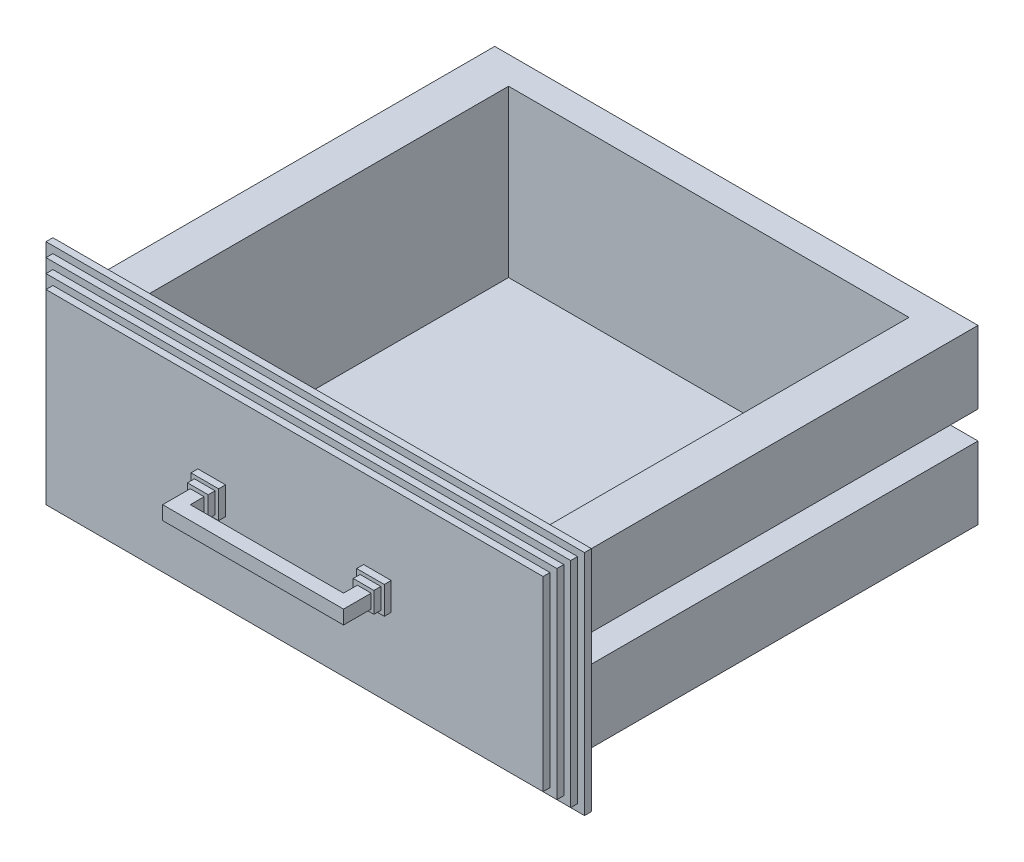
SolidWorks part; units mm, degrees
ref_plane "Front Plane" through (0, 0, 0) normal (0, 0, 1) x (1, 0, 0)
ref_plane "Top Plane" through (0, 0, 0) normal (0, 1, 0) x (1, 0, 0)
ref_plane "Right Plane" through (0, 0, 0) normal (1, 0, 0) x (0, 0, -1)
sketch "Sketch1" plane through (0, 0, 0) normal (0, 0, 1) x (1, 0, 0)
  line L0 (0, -415.8097) -> (0, 415.8097) construction
  line L1 (-175, 206.3609) -> (175, 206.3609)
  line L2 (-175, 206.3609) -> (-175, 258.8609)
  line L3 (-175, 331.3609) -> (175, 331.3609)
  line L4 (175, 206.3609) -> (175, 258.8609)
  line L5 (175, 258.8609) -> (155, 258.8609)
  line L6 (-175, 278.8609) -> (-155, 278.8609)
  line L7 (-175, 258.8609) -> (-155, 258.8609)
  line L8 (-155, 278.8609) -> (-155, 258.8609)
  line L9 (155, 278.8609) -> (155, 258.8609)
  line L10 (175, 278.8609) -> (155, 278.8609)
  line L11 (-175, 278.8609) -> (-175, 331.3609)
  line L12 (175, 278.8609) -> (175, 331.3609)
  dimension "D1" = 125
  dimension "D2" = 20
  dimension "D3" = 20
  dimension "D4" = 52.5
extrude "Boss-Extrude1" add sketch "Sketch1" along normal blind 320
sketch "Sketch2" plane through (0, 0, 320) normal (0, 0, 1) x (1, 0, 0)
  line L0 (0, 331.3609) -> (0, 206.3609) construction
  line L1 (175, 331.3609) -> (-175, 331.3609) construction
  line L2 (-175, 206.3609) -> (175, 206.3609) construction
  line L3 (-175, 278.8609) -> (155, 278.8609) construction
  line L4 (155, 258.8609) -> (-175, 258.8609) construction
  line L5 (70, 258.8609) -> (50, 258.8609)
  line L6 (-70, 278.8609) -> (-50, 278.8609)
  line L7 (-70, 278.8609) -> (-70, 258.8609)
  line L8 (-70, 258.8609) -> (-50, 258.8609)
  line L9 (-50, 278.8609) -> (-50, 258.8609)
  line L10 (50, 278.8609) -> (50, 258.8609)
  line L11 (70, 278.8609) -> (50, 278.8609)
  line L12 (70, 278.8609) -> (70, 258.8609)
  dimension "D1" = 20
  dimension "D2" = 50
extrude "Boss-Extrude2" add sketch "Sketch2" along normal blind 5
sketch "Sketch3" plane through (0, 0, 325) normal (0, 0, 1) x (1, 0, 0)
  line L0 (0, 331.3609) -> (0, 206.3609) construction
  line L1 (175, 331.3609) -> (-175, 331.3609) construction
  line L2 (-175, 206.3609) -> (175, 206.3609) construction
  line L3 (-161.3907, 268.8609) -> (0, 268.8609) construction
  line L4 (-60, 289.8862) -> (-60, 252.4462) construction
  line L5 (52.5, 276.3609) -> (67.5, 276.3609)
  line L6 (-52.5, 261.3609) -> (-67.5, 261.3609)
  line L7 (-52.5, 261.3609) -> (-52.5, 276.3609)
  line L8 (-52.5, 276.3609) -> (-67.5, 276.3609)
  line L9 (-67.5, 261.3609) -> (-67.5, 276.3609)
  line L10 (-52.5, 261.3609) -> (-67.5, 276.3609) construction
  line L11 (-52.5, 276.3609) -> (-67.5, 261.3609) construction
  line L12 (67.5, 261.3609) -> (67.5, 276.3609)
  line L13 (52.5, 261.3609) -> (67.5, 261.3609)
  line L14 (52.5, 261.3609) -> (52.5, 276.3609)
  point P10 (-60, 268.8609)
  dimension "D1" = 15
  dimension "D2" = 15
extrude "Boss-Extrude3" add sketch "Sketch3" along normal blind 5
sketch "Sketch4" plane through (0, 0, 330) normal (0, 0, 1) x (1, 0, 0)
  line L0 (0, 331.3609) -> (0, 206.3609) construction
  line L1 (175, 331.3609) -> (-175, 331.3609) construction
  line L2 (-175, 206.3609) -> (175, 206.3609) construction
  line L3 (-188.8492, 268.8609) -> (183.7972, 268.8609) construction
  line L4 (-60.4961, 250.6327) -> (-60.4961, 286.6802) construction
  line L5 (55.4961, 273.6564) -> (65.4961, 273.6564)
  line L6 (-55.4961, 263.6564) -> (-65.4961, 263.6564)
  line L7 (-55.4961, 263.6564) -> (-55.4961, 273.6564)
  line L8 (-55.4961, 273.6564) -> (-65.4961, 273.6564)
  line L9 (-65.4961, 263.6564) -> (-65.4961, 273.6564)
  line L10 (-55.4961, 263.6564) -> (-65.4961, 273.6564) construction
  line L11 (-55.4961, 273.6564) -> (-65.4961, 263.6564) construction
  line L12 (65.4961, 263.6564) -> (65.4961, 273.6564)
  line L13 (55.4961, 263.6564) -> (65.4961, 263.6564)
  line L14 (55.4961, 263.6564) -> (55.4961, 273.6564)
  point P10 (-60.4961, 268.6564)
  dimension "D1" = 10
  dimension "D2" = 10
extrude "Boss-Extrude4" add sketch "Sketch4" along normal blind 20
sketch "Sketch5" plane through (55.4961, 0, 0) normal (-1, 0, 0) x (0, 0, 1)
  line L0 (350, 263.6564) -> (330, 263.6564) construction
  line L1 (350, 273.6564) -> (340, 273.6564)
  line L2 (350, 273.6564) -> (350, 263.6564)
  line L3 (350, 263.6564) -> (340, 263.6564)
  line L4 (340, 273.6564) -> (340, 263.6564)
extrude "Boss-Extrude5" add sketch "Sketch5" along normal up to next
sketch "Sketch6" plane through (0, 331.3609, 0) normal (0, 1, 0) x (1, 0, 0)
  line L0 (175, -320) -> (-175, -320) construction
  line L1 (-145, -20) -> (145, -20)
  line L2 (-145, -20) -> (-145, -300)
  line L3 (-145, -300) -> (145, -300)
  line L4 (145, -20) -> (145, -300)
  line L5 (-175, -320) -> (-175, 0) construction
  line L6 (175, -320) -> (175, 0) construction
  line L7 (175, 0) -> (-175, 0) construction
  dimension "D1" = 20
  dimension "D2" = 30
  dimension "D3" = 30
  dimension "D4" = 20
extrude "Cut-Extrude1" cut sketch "Sketch6" against normal blind 120
sketch "Sketch7" plane through (0, 0, 320) normal (0, 0, 1) x (1, 0, 0)
  line L0 (0, 331.3609) -> (0, 206.3609) construction
  line L1 (175, 331.3609) -> (-175, 331.3609) construction
  line L2 (-175, 206.3609) -> (175, 206.3609) construction
  line L3 (-190.8635, 268.8609) -> (187.6824, 268.8609) construction
  line L4 (-175, 331.3609) -> (-175, 278.8609) construction
  line L5 (180, 336.3609) -> (-180, 336.3609)
  line L6 (180, 336.3609) -> (180, 201.3609)
  line L7 (180, 201.3609) -> (-180, 201.3609)
  line L8 (-180, 336.3609) -> (-180, 201.3609)
  line L9 (180, 336.3609) -> (-180, 201.3609) construction
  line L10 (180, 201.3609) -> (-180, 336.3609) construction
  point P8 (0, 268.8609)
  dimension "D1" = 5
  dimension "D3" = 5
extrude "Boss-Extrude6" add sketch "Sketch7" against normal blind 5
sketch "Sketch8" plane through (0, 0, 315) normal (0, 0, -1) x (-1, 0, 0)
  line L8 (185, 196.3609) -> (185, 341.3609)
  line L9 (185, 341.3609) -> (-185, 341.3609)
  line L10 (-185, 341.3609) -> (-185, 196.3609)
  line L11 (-185, 196.3609) -> (185, 196.3609)
  line L12 (185, 196.3609) -> (185, 341.3609)
  line L13 (185, 341.3609) -> (-185, 341.3609)
  line L14 (-185, 341.3609) -> (-185, 196.3609)
  line L15 (-185, 196.3609) -> (185, 196.3609)
  dimension "D1" = 5
extrude "Boss-Extrude7" add sketch "Sketch8" along normal blind 5
sketch "Sketch9" plane through (0, 0, 310) normal (0, 0, -1) x (-1, 0, 0)
  line L8 (-190, 191.3609) -> (190, 191.3609)
  line L9 (190, 191.3609) -> (190, 346.3609)
  line L10 (190, 346.3609) -> (-190, 346.3609)
  line L11 (-190, 346.3609) -> (-190, 191.3609)
  line L12 (-190, 191.3609) -> (190, 191.3609)
  line L13 (190, 191.3609) -> (190, 346.3609)
  line L14 (190, 346.3609) -> (-190, 346.3609)
  line L15 (-190, 346.3609) -> (-190, 191.3609)
  dimension "D1" = 5
extrude "Boss-Extrude8" add sketch "Sketch9" along normal blind 5
sketch "Sketch10" plane through (0, 0, 305) normal (0, 0, -1) x (-1, 0, 0)
  line L8 (-195, 351.3609) -> (-195, 186.3609)
  line L9 (-195, 186.3609) -> (195, 186.3609)
  line L10 (195, 186.3609) -> (195, 351.3609)
  line L11 (195, 351.3609) -> (-195, 351.3609)
  line L12 (-195, 351.3609) -> (-195, 186.3609)
  line L13 (-195, 186.3609) -> (195, 186.3609)
  line L14 (195, 186.3609) -> (195, 351.3609)
  line L15 (195, 351.3609) -> (-195, 351.3609)
  dimension "D1" = 5
extrude "Boss-Extrude9" add sketch "Sketch10" along normal blind 5
